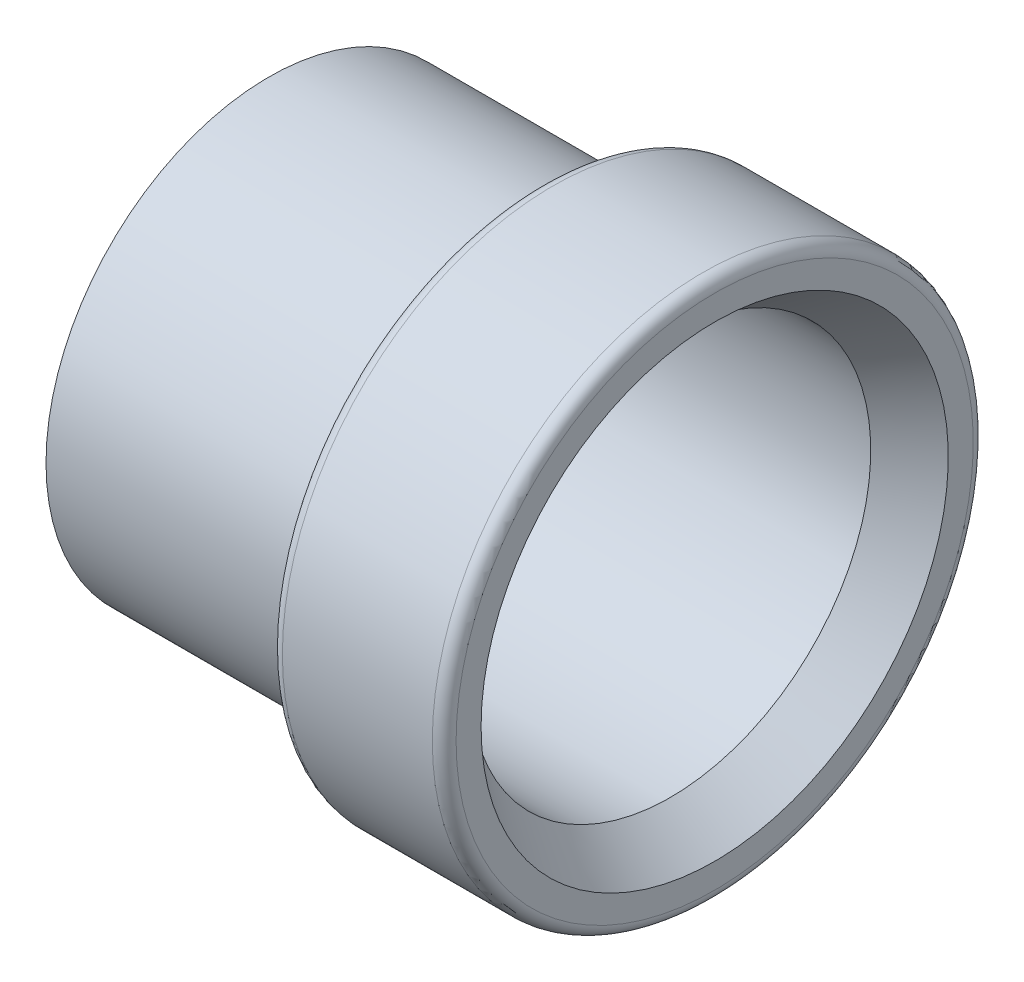
SolidWorks part; units mm, degrees
material "1060 Alloy"
ref_plane "Front Plane" through (0, 0, 0) normal (0, 0, 1) x (1, 0, 0)
ref_plane "Top Plane" through (0, 0, 0) normal (0, 1, 0) x (1, 0, 0)
ref_plane "Right Plane" through (0, 0, 0) normal (1, 0, 0) x (0, 0, -1)
sketch "Sketch1" plane through (0, 0, 0) normal (0, 0, 1) x (1, 0, 0)
  line L0 (-7.1374, 0) -> (7.1374, 0) construction
  line L1 (-7.1374, 6.4135) -> (5.7217, 6.4135)
  line L2 (5.7217, 6.4135) -> (7.1374, 7.4803)
  line L4 (7.1374, 7.4803) -> (7.1374, 8.2804)
  line L5 (6.7564, 8.6614) -> (1.9558, 8.6614)
  line L6 (1.5748, 8.2804) -> (1.5748, 7.1374)
  line L7 (1.5748, 7.1374) -> (-7.1374, 7.1374)
  line L8 (-7.1374, 6.4135) -> (-7.1374, 7.1374)
  arc A0 (7.1374, 8.2804) -> (6.7564, 8.6614) centre (6.7564, 8.2804) ccw
  arc A1 (1.9558, 8.6614) -> (1.5748, 8.2804) centre (1.9558, 8.2804) ccw
  point P12 (7.1374, 8.6614)
  point P15 (1.5748, 8.6614)
  dimension "D2" = 0.381
  dimension "D1" = 37
  dimension "M" = 14.2748
  dimension "G" = 17.3228
  dimension "J" = 5.5626
  dimension "B" = 12.827
  dimension "C" = 14.2748
  dimension "F" = 14.9606
revolve "Revolve1" add sketch "Sketch1" angle 360 about L0
